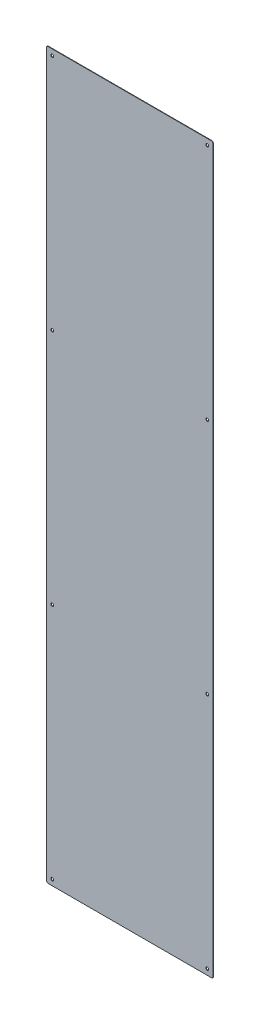
SolidWorks part; units mm, degrees
material "AISI 1045 Steel, cold drawn"
ref_plane "Front Plane" through (0, 0, 0) normal (0, 0, 1) x (1, 0, 0)
ref_plane "Top Plane" through (0, 0, 0) normal (0, 1, 0) x (1, 0, 0)
ref_plane "Right Plane" through (0, 0, 0) normal (1, 0, 0) x (0, 0, -1)
sketch "Sketch1" plane through (0, 0, 0) normal (0, 0, 1) x (1, 0, 0)
  line L1 (-185, 806.5) -> (185, 806.5)
  line L2 (-185, 806.5) -> (-185, -806.5)
  line L3 (-185, -806.5) -> (185, -806.5)
  line L4 (185, 806.5) -> (185, -806.5)
  line L5 (-185, 806.5) -> (185, -806.5) construction
  line L6 (-185, -806.5) -> (185, 806.5) construction
  point P0 (0, 0)
  dimension "D1" = 370
  dimension "D2" = 1613
extrude "Boss-Extrude1" add sketch "Sketch1" along normal blind 1
sketch "Sketch2" plane through (0, 0, 1) normal (0, 0, 1) x (1, 0, 0)
  line L0 (-185, -806.5) -> (185, -806.5) construction
  line L1 (-185, 806.5) -> (-185, -806.5) construction
  line L2 (0, -806.5) -> (0, -1557.3189) construction
  circle A0 centre (-172.5, -793.5) radius 3.25
  circle A1 centre (172.5, -793.5) radius 3.25
  dimension "D1" = 6.5
  dimension "D2" = 13
  dimension "D3" = 12.5
extrude "Cut-Extrude1" cut sketch "Sketch2" against normal up to next (1 mm away)
pattern_linear "LPattern1" count 4 spacing 529 along (0, 1, 0) of "Cut-Extrude1"
fillet "Fillet1" radius 3 4 edges at (185, -806.5, 0.5) (-185, -806.5, 0.5) (185, 806.5, 0.5) (-185, 806.5, 0.5)
